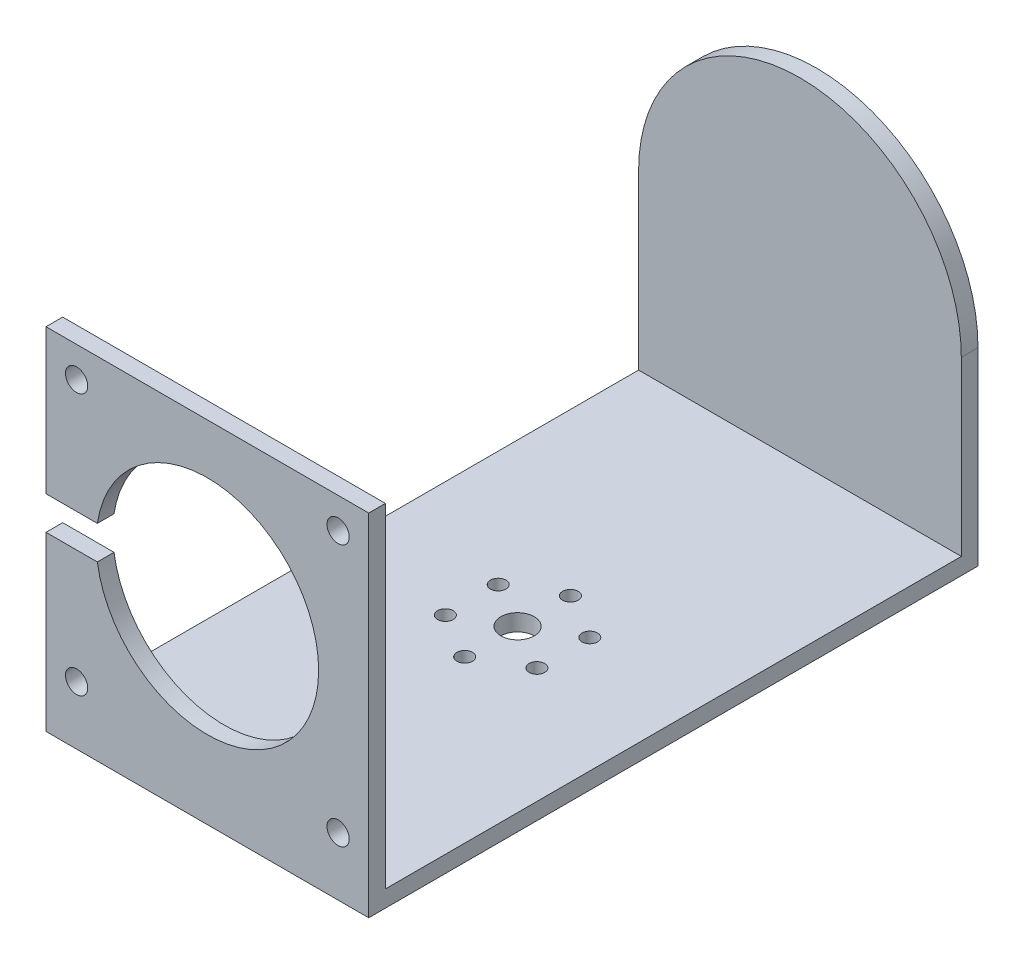
SolidWorks part; units mm, degrees
material "1060 Alloy"
ref_plane "Front Plane" through (0, 0, 0) normal (0, 0, 1) x (1, 0, 0)
ref_plane "Top Plane" through (0, 0, 0) normal (0, 1, 0) x (1, 0, 0)
ref_plane "Right Plane" through (0, 0, 0) normal (1, 0, 0) x (0, 0, -1)
sketch "Sketch1" plane through (0, 0, 0) normal (1, 0, 0) x (0, 0, -1)
  line L0 (-73.3517, 30.4008) -> (-73.3517, -29.5992)
  line L1 (-73.3517, -29.5992) -> (30.1483, -29.5992)
  line L2 (30.1483, -29.5992) -> (30.1483, 30.4008)
  line L3 (30.1483, 30.4008) -> (33.1483, 30.4008)
  line L4 (33.1483, 30.4008) -> (33.1483, -32.5992)
  line L5 (33.1483, -32.5992) -> (-76.3517, -32.5992)
  line L6 (-76.3517, -32.5992) -> (-76.3517, 30.4008)
  line L7 (-76.3517, 30.4008) -> (-73.3517, 30.4008)
  dimension "D1" = 60
  dimension "D2" = 103.5
  dimension "D3" = 3
  dimension "D4" = 63
  dimension "D5" = 109.5
extrude "Boss-Extrude1" add sketch "Sketch1" along normal blind 58
sketch "Sketch2" plane through (0, 0, 76.3517) normal (0, 0, 1) x (1, 0, 0)
  line L0 (0, 30.4008) -> (0, 24.9008) construction
  line L1 (0, 30.4008) -> (0, -32.5992) construction
  line L2 (0, 24.9008) -> (5.5, 24.9008) construction
  line L3 (29, 30.4008) -> (29, -32.5992) construction
  line L4 (58, 30.4008) -> (0, 30.4008) construction
  line L5 (58, -32.5992) -> (0, -32.5992) construction
  line L6 (58, 30.4008) -> (58, 1.4008) construction
  line L7 (58, 30.4008) -> (58, -32.5992) construction
  line L8 (58, 1.4008) -> (0, 1.4008) construction
  circle A0 centre (5.5, 24.9008) radius 2
  circle A1 centre (52.5, 24.9008) radius 2
  circle A2 centre (52.5, -22.0992) radius 2
  circle A3 centre (5.5, -22.0992) radius 2
  circle A4 centre (29, 1.4008) radius 20
  dimension "D4" = 4
  dimension "D5" = 40
  dimension "D1" = 5.5
  dimension "D2" = 5.5
  dimension "D3" = 29
extrude "Cut-Extrude1" cut sketch "Sketch2" against normal blind 58
sketch "Sketch3" plane through (0, 0, -33.1483) normal (0, 0, -1) x (-1, 0, 0)
  line L0 (-29, 30.4008) -> (-58, 30.4008)
  line L1 (-58, 30.4008) -> (0, 30.4008) construction
  line L2 (-58, 30.4008) -> (-58, 1.4008)
  line L3 (-58, -32.5992) -> (-58, 30.4008) construction
  arc A0 (-58, 1.4008) -> (-29, 30.4008) centre (-29, 1.4008) cw
  dimension "D1" = 29
extrude "Cut-Extrude2" cut sketch "Sketch3" against normal blind 58
sketch "Sketch4" plane through (0, 0, -33.1483) normal (0, 0, -1) x (-1, 0, 0)
  line L0 (-29, 30.4008) -> (0, 30.4008)
  line L1 (-29, 30.4008) -> (0, 30.4008) construction
  line L2 (0, 30.4008) -> (0, 1.4008)
  line L3 (0, -32.5992) -> (0, 30.4008) construction
  arc A0 (0, 1.4008) -> (-29, 30.4008) centre (-29, 1.4008) ccw
  arc A1 (-29, 30.4008) -> (-58, 1.4008) centre (-29, 1.4008) ccw construction
  dimension "D1" = 29
extrude "Cut-Extrude3" cut sketch "Sketch4" against normal blind 58
sketch "Sketch5" plane through (0, 0, -33.1483) normal (0, 0, -1) x (-1, 0, 0)
  circle A0 centre (-29, 1.4008) radius 2.95
  dimension "D1" = 5.9
extrude "Boss-Extrude2" add sketch "Sketch5" along normal blind 8
sketch "Sketch6" plane through (0, -32.5992, 0) normal (0, -1, 0) x (1, 0, 0)
  circle A0 centre (29, 20.6017) radius 3
  circle A2 centre (29, 30.1017) radius 1.4
  circle A3 centre (37.2272, 25.3517) radius 1.4
  circle A4 centre (37.2272, 15.8517) radius 1.4
  circle A5 centre (29, 11.1017) radius 1.4
  circle A6 centre (20.7728, 15.8517) radius 1.4
  circle A7 centre (20.7728, 25.3517) radius 1.4
  point P17 (29, 20.6017)
  dimension "D1" = 6
  dimension "D3" = 2.8
  dimension "D4" = 6
extrude "Cut-Extrude4" cut sketch "Sketch6" against normal blind 8
sketch "Sketch7" plane through (0, 0, 76.3517) normal (0, 0, 1) x (1, 0, 0)
  line L0 (29, 1.4008) -> (29, 4.4008) construction
  line L1 (29, 4.4008) -> (0, 4.4008)
  line L2 (0, 30.4008) -> (0, -32.5992) construction
  line L3 (29, 4.4008) -> (29, -1.5992)
  line L4 (29, -1.5992) -> (0, -1.5992)
  line L5 (0, -1.5992) -> (0, 4.4008)
  dimension "D1" = 3
  dimension "D2" = 6
extrude "Cut-Extrude5" cut sketch "Sketch7" against normal blind 10
